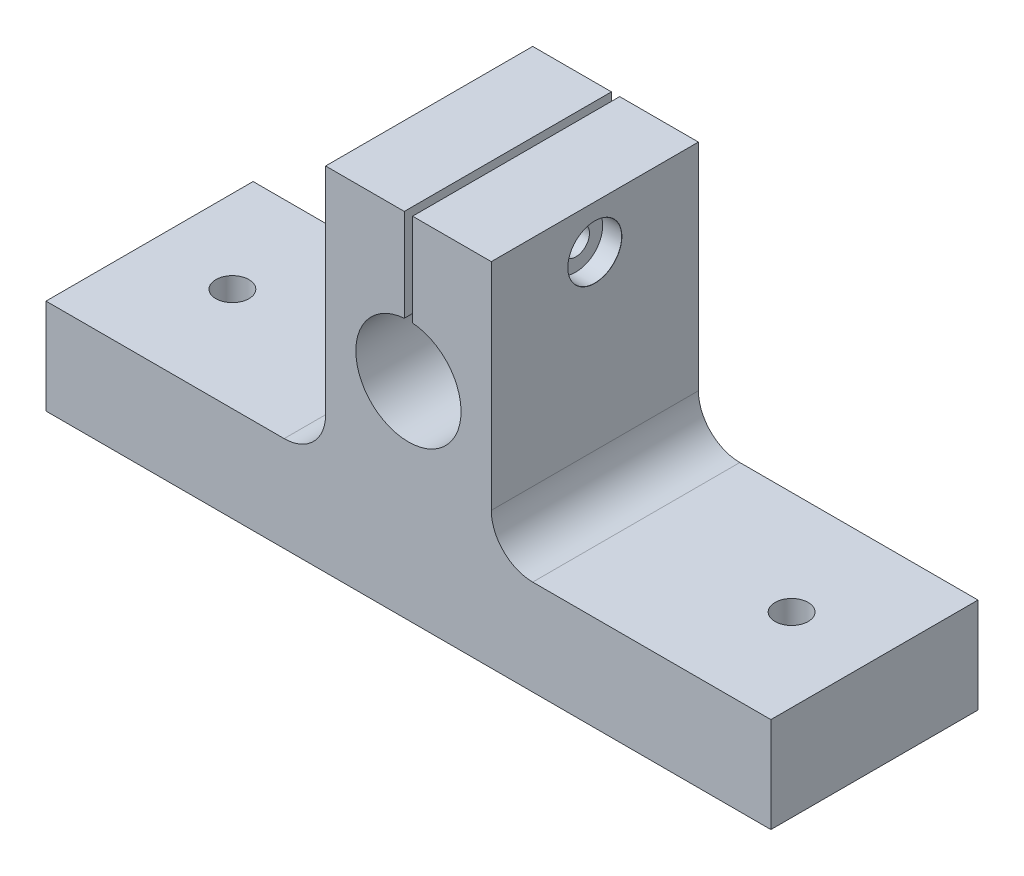
SolidWorks part; units mm, degrees
material "Aço carbono simples"
ref_plane "Plano frontal" through (0, 0, 0) normal (0, 0, 1) x (1, 0, 0)
ref_plane "Plano superior" through (0, 0, 0) normal (0, 1, 0) x (1, 0, 0)
ref_plane "Plano direito" through (0, 0, 0) normal (1, 0, 0) x (0, 0, -1)
sketch "Esboço1" plane through (0, 0, 0) normal (0, 0, 1) x (1, 0, 0)
  line L0 (0, 103.072) -> (0, -55.6144) construction
  line L1 (87.5, 0) -> (-87.5, 0)
  line L2 (-87.5, 0) -> (-87.5, 23)
  line L3 (-87.5, 23) -> (-20, 23)
  line L4 (-20, 23) -> (-20, 85)
  line L5 (-20, 85) -> (20, 85)
  line L6 (20, 23) -> (20, 85)
  line L7 (87.5, 23) -> (20, 23)
  line L8 (87.5, 0) -> (87.5, 23)
  point P9 (0, 85)
  point P13 (0, 0)
  dimension "D1" = 87.5
  dimension "D2" = 23
  dimension "D3" = 20
  dimension "D4" = 85
extrude "Ressalto-extrusão1" add sketch "Esboço1" along normal blind 50
sketch "Esboço2" plane through (0, 23, 0) normal (0, 1, 0) x (1, 0, 0)
  line L0 (-87.5, -25) -> (87.5, -25) construction
  line L1 (-87.5, -50) -> (-87.5, 0) construction
  line L2 (87.5, -50) -> (87.5, 0) construction
  line L3 (0, 0) -> (0, -50) construction
  line L4 (20, -50) -> (-20, -50) construction
  circle A0 centre (-67.5, -25) radius 4
  circle A2 centre (67.5, -25) radius 4
  dimension "D1" = 8
  dimension "D2" = 20
extrude "Corte-extrusão1" cut sketch "Esboço2" against normal through all
sketch "Esboço3" plane through (0, 0, 50) normal (0, 0, 1) x (1, 0, 0)
  line L0 (0, -8.8694) -> (0, 56.5) construction
  line L1 (20, 85) -> (-20, 85) construction
  line L2 (1, 56.5) -> (-1, 56.5)
  line L3 (1, 62.6606) -> (1, 116.5)
  line L4 (1, 116.5) -> (-1, 116.5)
  line L5 (-1, 62.6606) -> (-1, 116.5)
  line L6 (0, 85) -> (-1, 116.5) construction
  line L7 (1, 116.5) -> (0, 85) construction
  line L8 (-87.5, 0) -> (87.5, 0) construction
  line L9 (0, 61.2) -> (0, 97.6746) construction
  arc A0 (-1, 62.6606) -> (1, 62.6606) centre (0, 50) ccw
  point P5 (0, 85)
  dimension "D1" = 25.4
  dimension "D3" = 50
  dimension "D2" = 60
  dimension "D4" = 2
extrude "Corte-extrusão2" cut sketch "Esboço3" against normal through all
fillet "Filete1" radius 10 2 edges at (-20, 23, 25) (20, 23, 25)
hole_wizard "Rebaixo para parafuso de máquina com cabeça panela de M61" positions "Esboço4" profile "Esboço5" counterbore size "M6" standard "Ansi Metric" end condition through all
sketch "Esboço4" plane through (20, 0, 0) normal (1, 0, 0) x (0, 0, -1)
  line L0 (-50, 85) -> (0, 85) construction
  line L1 (-25, 90.1684) -> (-25, 35.2893) construction
  point P0 (-25, 74.5)
  point P9 (0, 0)
  dimension "D1" = 10.5
sketch "Esboço5" plane through (20, 74.5, 25) normal (0, 1, 0) x (0, 0, -1)
  line L0 (0, 0) -> (0, 107.5)
  line L1 (0, 107.5) -> (3.3, 107.5)
  line L3 (3.3, 107.5) -> (3.3, 4.6)
  line L4 (6.5, 4.6) -> (3.3, 4.6)
  line L5 (6.5, 4.6) -> (6.5, 0.025)
  line L6 (6.5, 0.025) -> (6.525, 0)
  line L7 (6.525, 0) -> (0, 0)
  line L8 (-6.5, 0.025) -> (-6.525, 0) construction
  line L11 (0, -6.35) -> (0, 107.95) construction
  dimension "Thru Hole Dia." = 6.6
  dimension "Thru Hole Depth" = 107.5
  dimension "C'Bore Dia." = 13
  dimension "C'Bore Depth" = 4.6
  dimension "Near C'Sink Dia." = 13.05
  dimension "Near C'Sink Angle" = 90
